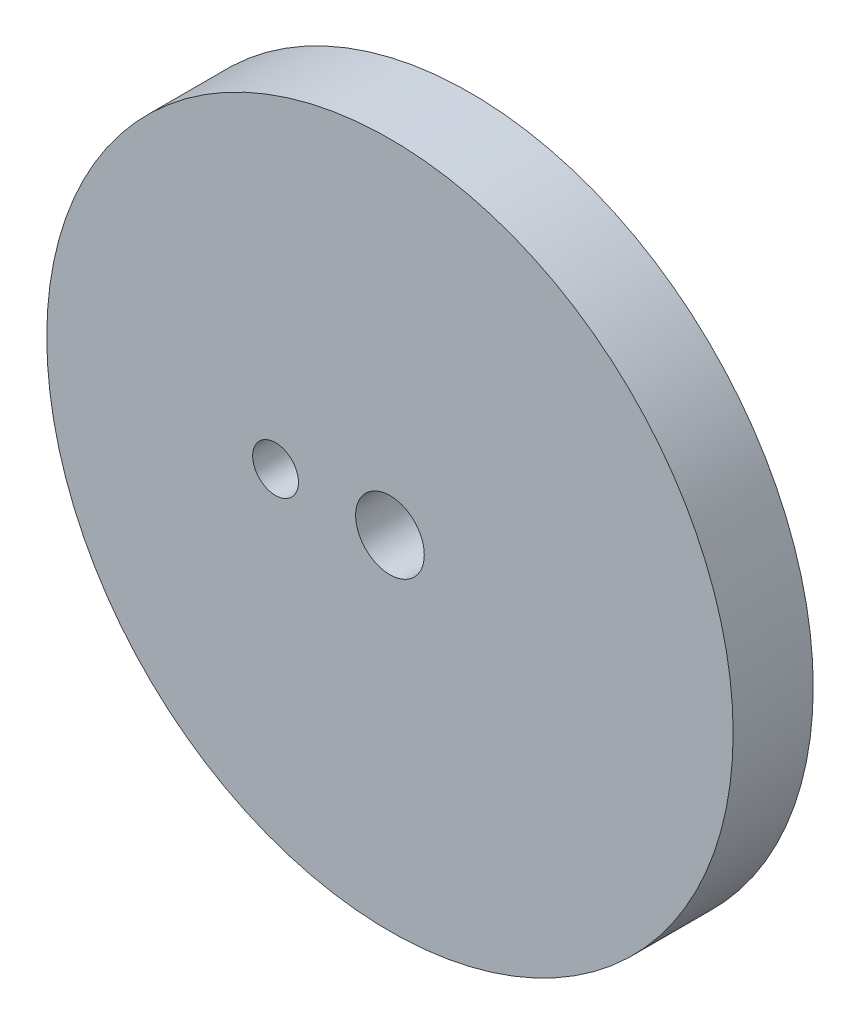
SolidWorks part; units mm, degrees
ref_plane "Plan de face" through (0, 0, 0) normal (0, 0, 1) x (1, 0, 0)
ref_plane "Plan de dessus" through (0, 0, 0) normal (0, 1, 0) x (1, 0, 0)
ref_plane "Plan de droite" through (0, 0, 0) normal (1, 0, 0) x (0, 0, -1)
sketch "Esquisse1" plane through (0, 0, 0) normal (0, 0, 1) x (1, 0, 0)
  circle A0 centre (0, 0) radius 30
  circle A1 centre (0, 0) radius 3
  circle A2 centre (-10, 0) radius 2
  dimension "D1" = 60
  dimension "D2" = 6
  dimension "D3" = 4
  dimension "D4" = 10
extrude "Extrusion1" add sketch "Esquisse1" along normal blind 7
